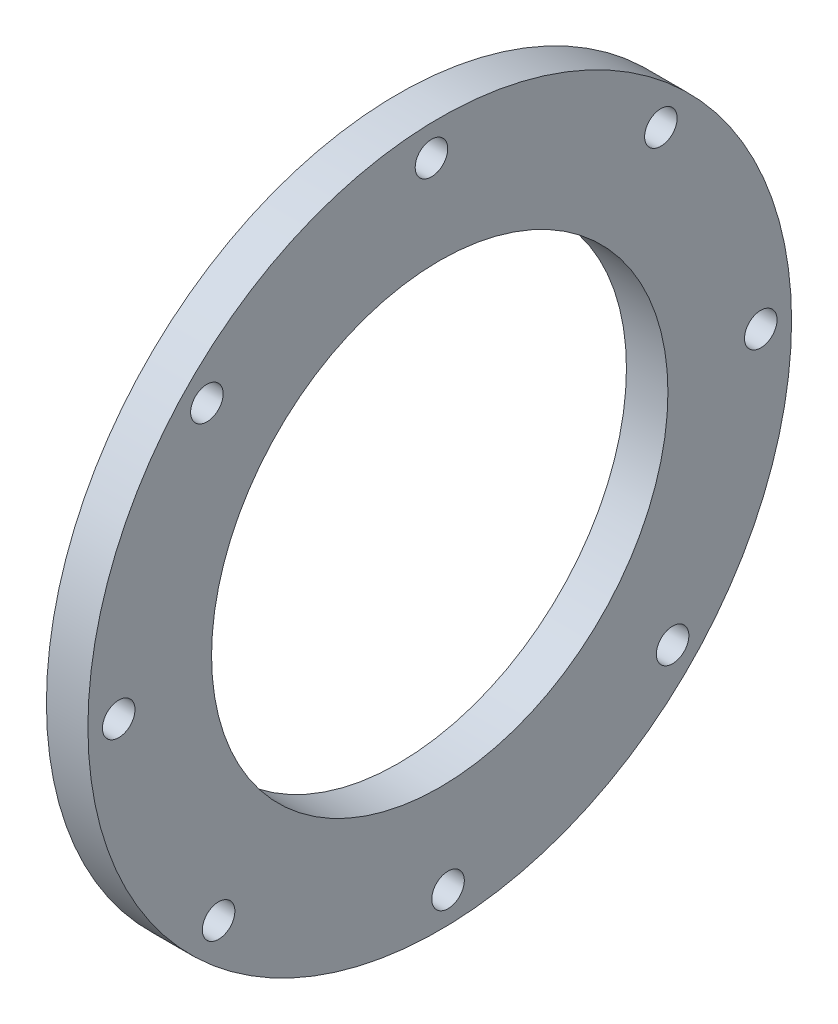
SolidWorks part; units mm, degrees
material "AISI 304"
ref_plane "Front Plane" through (0, 0, 0) normal (0, 0, 1) x (1, 0, 0)
ref_plane "Top Plane" through (0, 0, 0) normal (0, 1, 0) x (1, 0, 0)
ref_plane "Right Plane" through (0, 0, 0) normal (1, 0, 0) x (0, 0, -1)
sketch "Sketch1" plane through (-88.9, 0, 0) normal (-1, 0, 0) x (0, 0, 1)
  circle A0 centre (0, 0) radius 53.848
  circle A1 centre (0, 0) radius 34.925
  circle A2 centre (-33.8451, 35.6389) radius 2.4892
  circle A3 centre (1.2684, 49.1326) radius 2.4892
  circle A4 centre (35.6389, 33.8451) radius 2.4892
  circle A5 centre (49.1326, -1.2684) radius 2.4892
  circle A6 centre (33.8451, -35.6389) radius 2.4892
  circle A7 centre (-1.2684, -49.1326) radius 2.4892
  circle A8 centre (-35.6389, -33.8451) radius 2.4892
  circle A9 centre (-49.1326, 1.2684) radius 2.4892
  dimension "D2" = 69.85
  dimension "D3" = 4.9784
  dimension "D1" = 8
extrude "Boss-Extrude1" add sketch "Sketch1" along normal blind 6.35
